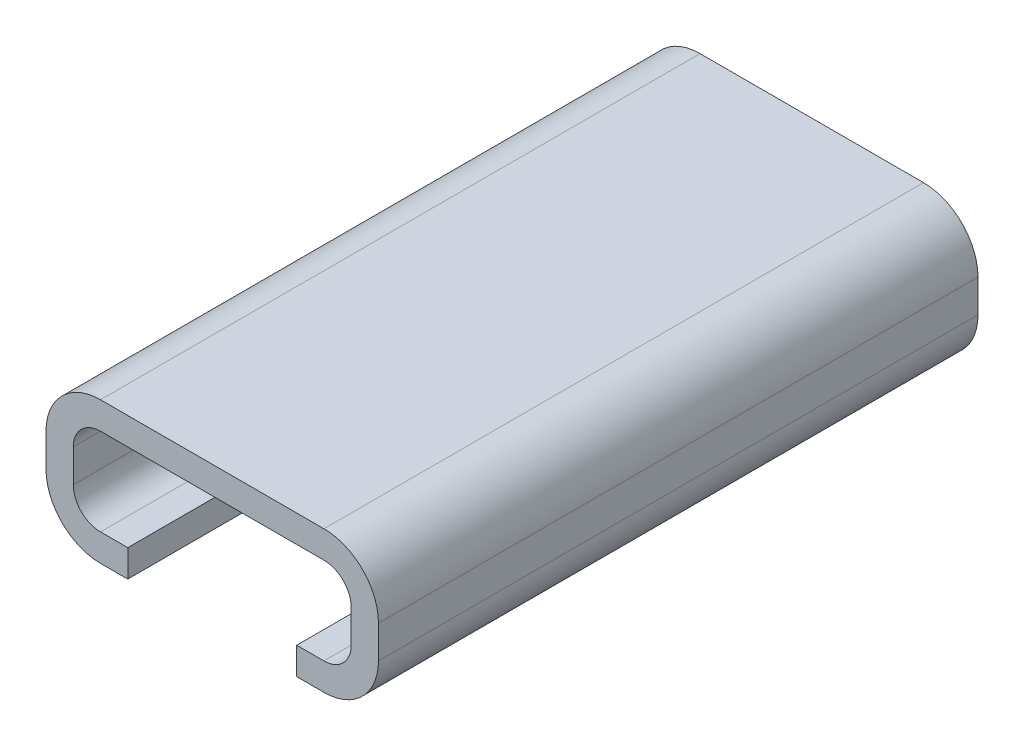
SolidWorks part; units mm, degrees
ref_plane "Plan de face" through (0, 0, 0) normal (0, 0, 1) x (1, 0, 0)
ref_plane "Plan de dessus" through (0, 0, 0) normal (0, 1, 0) x (1, 0, 0)
ref_plane "Plan de droite" through (0, 0, 0) normal (1, 0, 0) x (0, 0, -1)
sketch "Esquisse1" plane through (0, 0, 0) normal (0, 0, 1) x (1, 0, 0)
  line L1 (5.1, 0.6) -> (5.1, -0.6)
  line L2 (4.1, -1.6) -> (-4.1, -1.6)
  line L3 (-5.1, -0.6) -> (-5.1, 0.6)
  line L5 (6.1, 0.6) -> (6.1, -0.6)
  line L6 (4.1, -2.6) -> (-4.1, -2.6)
  line L7 (-6.1, -0.6) -> (-6.1, 0.6)
  line L16 (-4.1, 2.6) -> (4.1, 2.6) construction
  line L17 (4.1, 2.6) -> (-2.3321, 2.6)
  line L18 (-4.1, 2.6) -> (-2.3321, 2.6)
  line L19 (-4.1, 1.6) -> (4.1, 1.6)
  line L20 (-4.1, 1.6) -> (4.1, 1.6) construction
  arc A0 (-4.1, -1.6) -> (-5.1, -0.6) centre (-4.1, -0.6) cw
  arc A1 (5.1, -0.6) -> (4.1, -1.6) centre (4.1, -0.6) cw
  arc A2 (4.1, 1.6) -> (5.1, 0.6) centre (4.1, 0.6) cw
  arc A3 (-4.1, 1.6) -> (-5.1, 0.6) centre (-4.1, 0.6) ccw
  arc A4 (4.1, 2.6) -> (6.1, 0.6) centre (4.1, 0.6) cw
  arc A5 (6.1, -0.6) -> (4.1, -2.6) centre (4.1, -0.6) cw
  arc A6 (-4.1, -2.6) -> (-6.1, -0.6) centre (-4.1, -0.6) cw
  arc A7 (-4.1, 2.6) -> (-6.1, 0.6) centre (-4.1, 0.6) ccw
  point P6 (-5.1, -1.6)
  point P11 (5.1, 1.6)
  point P14 (-5.1, 1.6)
  point P15 (0, 1.6)
  point P16 (-5.1, 0)
  dimension "D3" = 1
  dimension "D1" = 3.2
  dimension "D2" = 10.2
  dimension "D9" = 3.2
  dimension "D4" = 1
extrude "Boss.-Extru.2" add sketch "Esquisse1" along normal blind 10
sketch "Esquisse7" plane through (0, 0, 0) normal (0, 0, -1) x (-1, 0, 0)
  line L8 (-6.1, 0.6) -> (-6.1, -0.6)
  line L9 (-4.1, -2.6) -> (4.1, -2.6)
  line L10 (6.1, -0.6) -> (6.1, 0.6)
  line L11 (4.1, 2.6) -> (-4.1, 2.6)
  line L16 (-6.1, 0.6) -> (-6.1, -0.6)
  line L17 (-4.1, -2.6) -> (4.1, -2.6)
  line L18 (6.1, -0.6) -> (6.1, 0.6)
  line L19 (4.1, 2.6) -> (-4.1, 2.6)
  arc A8 (-4.1, 2.6) -> (-6.1, 0.6) centre (-4.1, 0.6) ccw
  arc A9 (-6.1, -0.6) -> (-4.1, -2.6) centre (-4.1, -0.6) ccw
  arc A10 (4.1, -2.6) -> (6.1, -0.6) centre (4.1, -0.6) ccw
  arc A11 (6.1, 0.6) -> (4.1, 2.6) centre (4.1, 0.6) ccw
  arc A16 (-4.1, 2.6) -> (-6.1, 0.6) centre (-4.1, 0.6) ccw
  arc A17 (-6.1, -0.6) -> (-4.1, -2.6) centre (-4.1, -0.6) ccw
  arc A18 (4.1, -2.6) -> (6.1, -0.6) centre (4.1, -0.6) ccw
  arc A19 (6.1, 0.6) -> (4.1, 2.6) centre (4.1, 0.6) ccw
  dimension "D1" = 0
extrude "Boss.-Extru.4" add sketch "Esquisse7" along normal blind 1
mirror "Symétrie1" about plane through (4.1, 0.6, -1) normal (0, 0, -1) of "Boss.-Extru.4", "Boss.-Extru.2"
sketch "Esquisse5" plane through (0, -2.6, 0) normal (0, -1, 0) x (1, 0, 0)
  line L0 (4.1, -12) -> (-4.1, -12) construction
  line L1 (3.1, -12) -> (-3.1, -12)
  line L2 (3.1, -12) -> (3.1, -2)
  line L3 (3.1, -2) -> (-3.1, -2)
  line L4 (-3.1, -12) -> (-3.1, -2)
  line L5 (4.1, 10) -> (-4.1, 10) construction
  line L6 (-3.1, 10) -> (3.1, 10)
  line L7 (-3.1, 10) -> (-3.1, 0)
  line L8 (-3.1, 0) -> (3.1, 0)
  line L9 (3.1, 10) -> (3.1, 0)
  line L10 (-4.1, 10) -> (-4.1, -12) construction
  line L11 (4.1, 10) -> (4.1, -12) construction
  dimension "D1" = 10
  dimension "D2" = 10
  dimension "D3" = 1
  dimension "D4" = 1
extrude "Enlèv. mat.-Extru.1" cut sketch "Esquisse5" against normal up to surface (1 mm away) up to face at (0, -1.6, -7)
